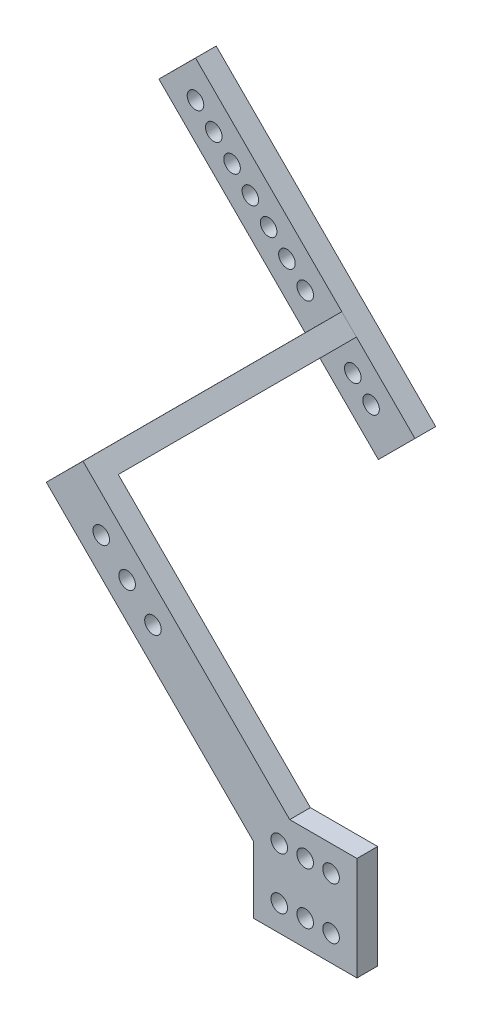
SolidWorks part; units mm, degrees
ref_plane "正面" through (0, 0, 0) normal (0, 0, 1) x (1, 0, 0)
ref_plane "平面" through (0, 0, 0) normal (0, 1, 0) x (1, 0, 0)
ref_plane "右側面" through (0, 0, 0) normal (1, 0, 0) x (0, 0, -1)
sketch "ｽｹｯﾁ1" plane through (0, 0, 0) normal (0, 0, 1) x (1, 0, 0)
  line L0 (-10.9947, -41.0833) -> (-50.9947, -1.0134)
  line L1 (-10.9947, -33.9485) -> (9.0053, -33.9485)
  line L2 (-10.9947, -33.9485) -> (-10.9947, -53.9485)
  line L3 (-10.9947, -53.9485) -> (9.0053, -53.9485)
  line L4 (9.0053, -33.9485) -> (9.0053, -53.9485)
  line L5 (-50.9947, -1.0134) -> (-43.9175, 6.0515)
  line L6 (-43.9175, 6.0515) -> (-3.9879, -33.9485)
  line L7 (-3.9879, -33.9485) -> (-10.9947, -41.0833)
  line L8 (-10.9947, -33.9485) -> (-9.8674, -33.9485)
  dimension "D1" = 20
  dimension "D2" = 20
  dimension "D3" = 10
  dimension "D4" = 10
  dimension "D5" = 40
  dimension "D6" = 40
extrude "ﾎﾞｽ - 押し出し1" add sketch "ｽｹｯﾁ1" along normal blind 4 contours L6 L7 L0 L5 | L2 L1 L4 L3
sketch "ｽｹｯﾁ2" plane through (0, 0, 4) normal (0, 0, 1) x (1, 0, 0)
  line L0 (-3.9879, -33.9485) -> (9.0053, -33.9485) construction
  line L1 (-10.9947, -41.0833) -> (-10.9947, -53.9485) construction
  circle A0 centre (-5.9947, -38.9485) radius 1.6
  circle A4 centre (-0.9947, -38.9485) radius 1.6
  circle A5 centre (4.0053, -38.9485) radius 1.6
  circle A6 centre (-0.9947, -48.9485) radius 1.6
  circle A7 centre (4.0053, -48.9485) radius 1.6
  circle A8 centre (-5.9947, -48.9485) radius 1.6
  dimension "D1" = 5
  dimension "D2" = 5
  dimension "D3" = 3
  dimension "D4" = 2
extrude "ｶｯﾄ - 押し出し1" cut sketch "ｽｹｯﾁ2" against normal blind 4
sketch "ｽｹｯﾁ3" plane through (0, 0, 4) normal (0, 0, 1) x (1, 0, 0)
  line L0 (-50.9947, -1.0134) -> (-43.9175, 6.0515) construction
  line L1 (-10.9947, -41.0833) -> (-50.9947, -1.0134) construction
  line L2 (-43.9175, 6.0515) -> (-3.9879, -33.9485) construction
  circle A0 centre (-40.3912, -4.5582) radius 1.6
  circle A1 centre (-35.3912, -9.567) radius 1.6
  circle A2 centre (-30.3912, -14.576) radius 1.6
  dimension "D1" = 3.2
  dimension "D2" = 3.2
  dimension "D4" = 5
  dimension "D5" = 10
  dimension "D6" = 5
  dimension "D9" = 3.2
  dimension "D10" = 5
  dimension "D11" = 5
  dimension "D12" = 5
extrude "ｶｯﾄ - 押し出し2" cut sketch "ｽｹｯﾁ3" against normal blind 4
sketch "ｽｹｯﾁ4" plane through (0, 0, 0) normal (0, 0, -1) x (-1, 0, 0)
  line L6 (43.9175, 6.0515) -> (50.9947, -1.0134)
  line L7 (50.9947, -1.0134) -> (48.1688, -3.8443)
  line L8 (10.9947, -41.0833) -> (50.9947, -1.0134) construction
  line L9 (48.1688, -3.8443) -> (41.0915, 3.2205)
  line L10 (43.9175, 6.0515) -> (3.9879, -33.9485) construction
  line L11 (41.0915, 3.2205) -> (43.9175, 6.0515)
  dimension "D1" = 4
extrude "ﾎﾞｽ - 押し出し2" add sketch "ｽｹｯﾁ4" along normal blind 50
sketch "ｽｹｯﾁ6" plane through (-24.9461, 24.9897, 0) normal (-0.7065, 0.7077, 0) x (0.7077, 0.7065, 0)
  line L0 (-36.8061, 50) -> (-26.8061, 50) construction
  line L1 (-36.8061, -4) -> (-36.8061, 50) construction
  circle A0 centre (-31.8061, 44) radius 1.6
  circle A16 centre (-31.8061, 37) radius 1.6
  circle A17 centre (-31.8061, 30) radius 1.6
  circle A18 centre (-31.8061, 23) radius 1.6
  circle A19 centre (-31.8061, 16) radius 1.6
  circle A20 centre (-31.8061, 9) radius 1.6
  circle A21 centre (-31.8061, 2) radius 1.6
  circle A26 centre (-31.8061, -26) radius 1.6 [skipped]
  circle A27 centre (-31.8061, -19) radius 1.6 [skipped]
  circle A28 centre (-31.8061, -12) radius 1.6 [skipped]
  circle A29 centre (-31.8061, -5) radius 1.6 [skipped]
  point P6 (0, 0)
  dimension "D1" = 3.2
  dimension "D4" = 5
  dimension "D2" = 6
  dimension "D3" = 11
extrude "ｶｯﾄ - 押し出し3" cut sketch "ｽｹｯﾁ6" against normal blind 4
sketch "ｽｹｯﾁ7" plane through (-24.9461, 24.9897, 0) normal (-0.7065, 0.7077, 0) x (0.7077, 0.7065, 0)
  line L0 (-36.8061, -4) -> (-36.8061, 50) construction
  line L1 (-26.8061, 50) -> (-36.8061, 50)
  line L2 (-26.8061, 50) -> (-26.8061, 46)
  line L3 (-26.8061, 46) -> (-36.8061, 46)
  line L4 (-36.8061, 50) -> (-36.8061, 46)
  dimension "D1" = 4
extrude "ﾎﾞｽ - 押し出し3" add sketch "ｽｹｯﾁ7" along normal blind 40 and the other way blind 20
sketch "ｽｹｯﾁ8" plane through (0, 0, -46) normal (0, 0, 1) x (1, 0, 0)
  line L0 (-79.2543, 27.2955) -> (-72.177, 34.3604) construction
  line L1 (-79.2543, 27.2955) -> (-50.9947, -1.0134) construction
  circle A0 centre (-72.1832, 27.2893) radius 1.6
  circle A1 centre (-68.6508, 23.7507) radius 1.6
  circle A2 centre (-65.1183, 20.2121) radius 1.6
  circle A3 centre (-61.5859, 16.6735) radius 1.6
  circle A4 centre (-58.0534, 13.1349) radius 1.6
  circle A5 centre (-54.521, 9.5962) radius 1.6
  circle A6 centre (-50.9885, 6.0576) radius 1.6
  circle A7 centre (-41.8042, -3.1428) radius 1.6
  circle A8 centre (-38.2717, -6.6814) radius 1.6
  dimension "D1" = 5
  dimension "D2" = 5
  dimension "D3" = 3.2
  dimension "D4" = 7
  dimension "D5" = 2
  dimension "D6" = 2
extrude "ｶｯﾄ - 押し出し4" cut sketch "ｽｹｯﾁ8" against normal blind 40
